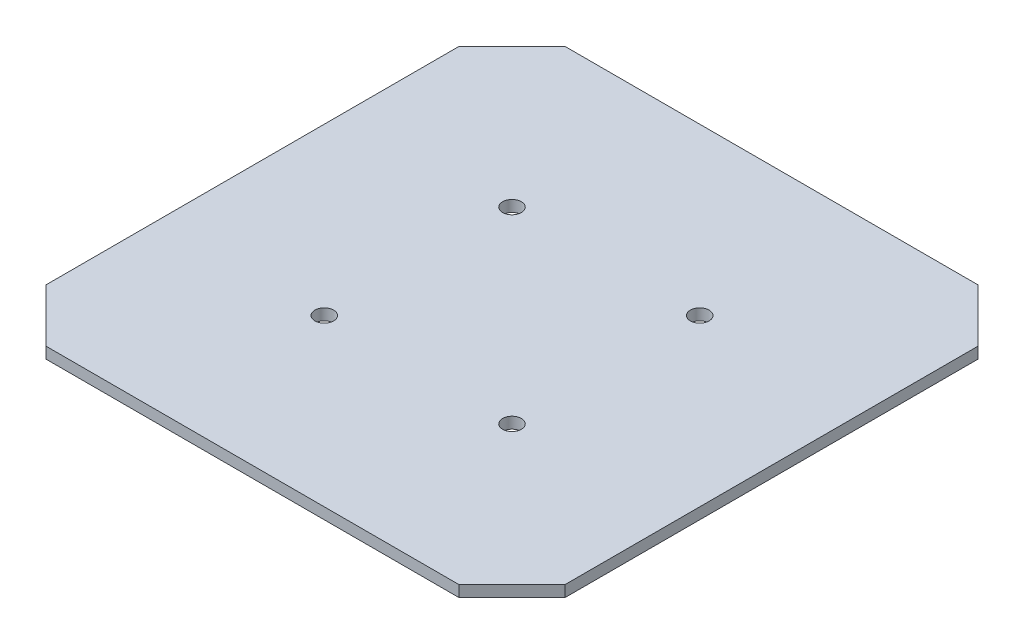
SolidWorks part; units mm, degrees
ref_plane "Front Plane" through (0, 0, 0) normal (0, 0, 1) x (1, 0, 0)
ref_plane "Top Plane" through (0, 0, 0) normal (0, 1, 0) x (1, 0, 0)
ref_plane "Right Plane" through (0, 0, 0) normal (1, 0, 0) x (0, 0, -1)
sketch "Sketch1" plane through (0, 0, 0) normal (0, 1, 0) x (1, 0, 0)
  line L0 (-69.1421, 55) -> (-55, 69.1421)
  line L1 (-55, 69.1421) -> (55, 69.1421)
  line L2 (-69.1421, 55) -> (-69.1421, -55)
  line L3 (-55, -69.1421) -> (55, -69.1421)
  line L4 (69.1421, 55) -> (69.1421, -55)
  line L5 (-69.1421, 69.1421) -> (69.1421, -69.1421) construction
  line L6 (-69.1421, -69.1421) -> (69.1421, 69.1421) construction
  line L7 (55, 69.1421) -> (69.1421, 55)
  line L8 (-69.1421, -55) -> (-55, -69.1421)
  line L9 (55, -69.1421) -> (69.1421, -55)
  line L10 (-69.1421, 69.1421) -> (-55, 69.1421) construction
  line L11 (-69.1421, 69.1421) -> (-69.1421, 55) construction
  line L12 (55, 69.1421) -> (69.1421, 69.1421) construction
  line L13 (69.1421, 69.1421) -> (69.1421, 55) construction
  line L14 (69.1421, -55) -> (69.1421, -69.1421) construction
  line L15 (69.1421, -69.1421) -> (55, -69.1421) construction
  line L16 (-69.1421, -69.1421) -> (-55, -69.1421) construction
  line L17 (-69.1421, -69.1421) -> (-69.1421, -55) construction
  line L18 (55, -69.1421) -> (40.8579, -55)
  line L19 (40.8579, -55) -> (55, -40.8579)
  line L20 (55, -40.8579) -> (69.1421, -55)
  line L21 (-69.1421, -55) -> (-55, -40.8579)
  line L22 (-55, -40.8579) -> (-40.8579, -55)
  line L23 (-40.8579, -55) -> (-55, -69.1421)
  line L24 (69.1421, 55) -> (55, 40.8579)
  line L25 (55, 40.8579) -> (40.8579, 55)
  line L26 (40.8579, 55) -> (55, 69.1421)
  line L27 (-55, 69.1421) -> (-40.8579, 55)
  line L28 (-40.8579, 55) -> (-55, 40.8579)
  line L29 (-55, 40.8579) -> (-69.1421, 55)
  circle A0 centre (-25, 25) radius 2.5
  circle A1 centre (25, 25) radius 2.5
  circle A2 centre (25, -25) radius 2.5
  circle A3 centre (-25, -25) radius 2.5
  point P0 (0, 0)
  dimension "D16" = 5
  dimension "D17" = 5
  dimension "D18" = 5
  dimension "D19" = 5
  dimension "D2" = 110
  dimension "D3" = 20
  dimension "D4" = 20
  dimension "D5" = 20
  dimension "D6" = 20
  dimension "D7" = 90
  dimension "D8" = 90
  dimension "D9" = 90
  dimension "D10" = 90
  dimension "D11" = 110
  dimension "D12" = 20
  dimension "D13" = 20
  dimension "D14" = 20
  dimension "D15" = 20
  dimension "D20" = 25
  dimension "D21" = 25
  dimension "D22" = 25
  dimension "D23" = 25
extrude "Boss-Extrude2" add sketch "Sketch1" along normal blind 3 contours L23 L22 L21 L8 | L28 L29 L2 L21 L22 L23 L3 L18 L19 L20 L4 L24 L25 L26 L1 L27 | L29 L28 L27 L0 | L26 L25 L24 L7 | L20 L19 L18 L9
